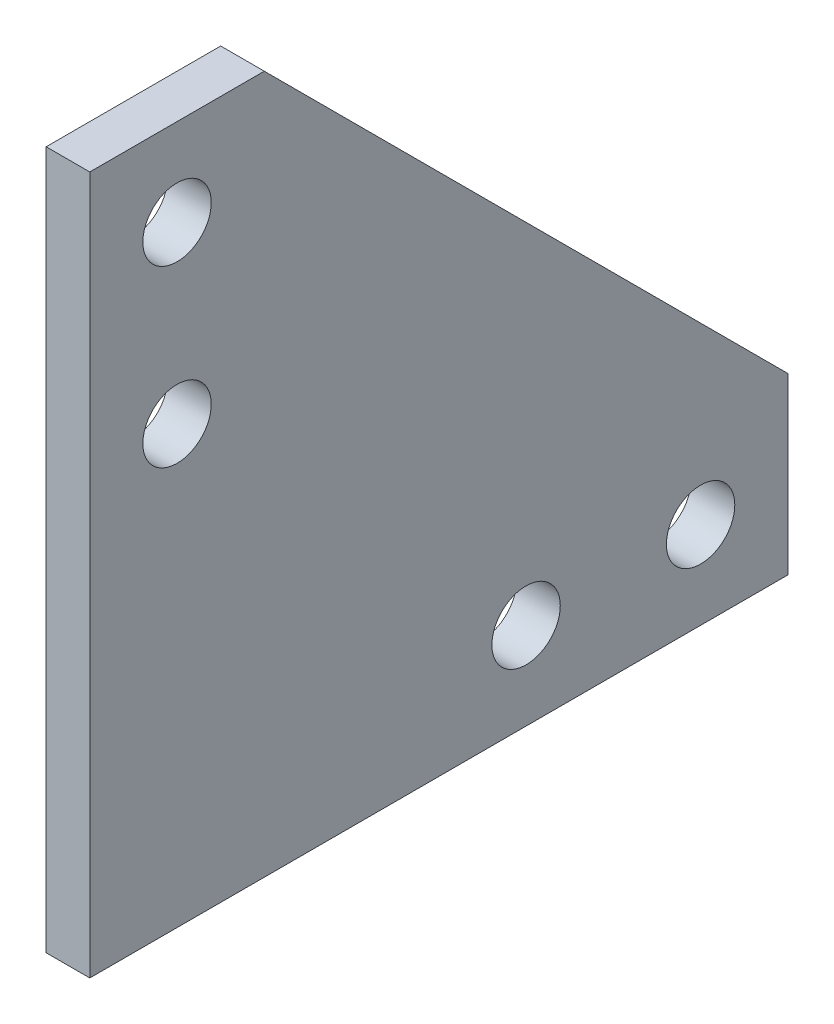
SolidWorks part; units mm, degrees
ref_plane "Front Plane" through (0, 0, 0) normal (0, 0, 1) x (1, 0, 0)
ref_plane "Top Plane" through (0, 0, 0) normal (0, 1, 0) x (1, 0, 0)
ref_plane "Right Plane" through (0, 0, 0) normal (1, 0, 0) x (0, 0, -1)
sketch "Sketch3" plane through (0, 0, 0) normal (1, 0, 0) x (0, 0, -1)
  line L0 (0, 0) -> (50.8, 0)
  line L1 (50.8, 0) -> (50.8, 12.7)
  line L2 (50.8, 12.7) -> (12.7, 50.8)
  line L3 (12.7, 50.8) -> (0, 50.8)
  line L4 (0, 50.8) -> (0, 0)
  circle A0 centre (6.35, 44.45) radius 2.4892
  circle A1 centre (6.35, 31.75) radius 2.4892
  circle A2 centre (31.75, 6.35) radius 2.4892
  circle A3 centre (44.45, 6.35) radius 2.4892
  point P14 (0, 0)
  point P15 (50.8, 6.35)
  point P16 (6.35, 50.8)
  dimension "D5" = 6.35
  dimension "D9" = 4.9784
  dimension "D1" = 45
  dimension "D2" = 50.8
  dimension "D3" = 50.8
  dimension "D4" = 12.7
  dimension "D6" = 12.7
  dimension "D7" = 12.7
  dimension "D8" = 6.35
extrude "Boss-Extrude1" add sketch "Sketch3" along normal blind 3.175
equation "\"Thick\"= \"in\""
